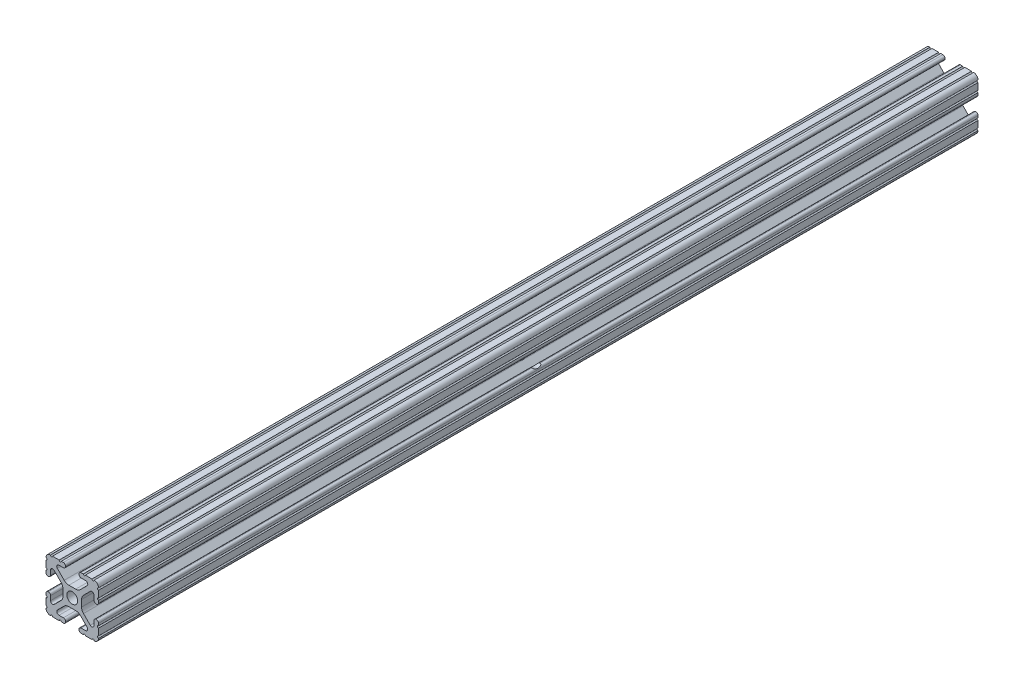
SolidWorks part; units mm, degrees
ref_plane "Front Plane" through (0, 0, 0) normal (0, 0, 1) x (1, 0, 0)
ref_plane "Top Plane" through (0, 0, 0) normal (0, 1, 0) x (1, 0, 0)
ref_plane "Right Plane" through (0, 0, 0) normal (1, 0, 0) x (0, 0, -1)
sketch "Sketch1" plane through (0, 0, 0) normal (0, 0, 1) x (1, 0, 0)
  line L88 (-7.1797, -8.6452) -> (-3.9523, -5.4237)
  line L89 (-1.7093, -4.4958) -> (1.7093, -4.4958)
  line L90 (3.9523, -5.4237) -> (7.1797, -8.6452)
  line L91 (6.4164, -10.4902) -> (4.2875, -10.4902)
  line L92 (3.2385, -11.5392) -> (3.2385, -11.651)
  line L93 (4.2875, -12.7) -> (5.3171, -12.7)
  line L94 (6.3331, -12.7) -> (9.5504, -12.7)
  line L95 (12.7, -9.5504) -> (12.7, -6.3331)
  line L96 (12.7, -5.3171) -> (12.7, -4.2875)
  line L97 (11.651, -3.2385) -> (11.5392, -3.2385)
  line L98 (10.4902, -4.2875) -> (10.4902, -6.4021)
  line L99 (8.7371, -7.1294) -> (5.441, -3.8408)
  line L100 (4.5085, -1.5932) -> (4.5085, 1.5932)
  line L101 (5.441, 3.8408) -> (8.7371, 7.1294)
  line L102 (10.4902, 6.4021) -> (10.4902, 4.2875)
  line L103 (11.5392, 3.2385) -> (11.651, 3.2385)
  line L104 (12.7, 4.2875) -> (12.7, 5.3171)
  line L105 (12.7, 6.3331) -> (12.7, 9.5504)
  line L106 (9.5504, 12.7) -> (6.3331, 12.7)
  line L107 (5.3171, 12.7) -> (4.2875, 12.7)
  line L108 (3.2385, 11.651) -> (3.2385, 11.5392)
  line L109 (4.2875, 10.4902) -> (6.4768, 10.4902)
  line L110 (7.207, 8.7244) -> (3.8983, 5.4232)
  line L111 (1.6558, 4.4958) -> (-1.6558, 4.4958)
  line L112 (-3.8983, 5.4232) -> (-7.207, 8.7244)
  line L113 (-6.4768, 10.4902) -> (-4.2875, 10.4902)
  line L114 (-3.2385, 11.5392) -> (-3.2385, 11.651)
  line L115 (-4.2875, 12.7) -> (-5.3171, 12.7)
  line L116 (-6.3331, 12.7) -> (-9.5504, 12.7)
  line L117 (-12.7, 9.5504) -> (-12.7, 6.3331)
  line L118 (-12.7, 5.3171) -> (-12.7, 4.2875)
  line L119 (-11.651, 3.2385) -> (-11.5392, 3.2385)
  line L120 (-10.4902, 4.2875) -> (-10.4902, 6.4021)
  line L121 (-8.7371, 7.1294) -> (-5.441, 3.8408)
  line L122 (-4.5085, 1.5932) -> (-4.5085, -1.5932)
  line L123 (-5.441, -3.8408) -> (-8.7371, -7.1294)
  line L124 (-10.4902, -6.4021) -> (-10.4902, -4.2875)
  line L125 (-11.5392, -3.2385) -> (-11.651, -3.2385)
  line L126 (-12.7, -4.2875) -> (-12.7, -5.3171)
  line L127 (-12.7, -6.3331) -> (-12.7, -9.5504)
  line L128 (-9.5504, -12.7) -> (-6.3331, -12.7)
  line L129 (-5.3171, -12.7) -> (-4.2875, -12.7)
  line L130 (-3.2385, -11.651) -> (-3.2385, -11.5392)
  line L131 (-4.2875, -10.4902) -> (-6.4164, -10.4902)
  circle A1 centre (0, 0) radius 2.6035
  arc A104 (-7.1797, -8.6452) -> (-6.4164, -10.4902) centre (-6.4164, -9.4098) ccw
  arc A105 (-1.7093, -4.4958) -> (-3.9523, -5.4237) centre (-1.7093, -7.6708) ccw
  arc A106 (3.9523, -5.4237) -> (1.7093, -4.4958) centre (1.7093, -7.6708) ccw
  arc A107 (6.4164, -10.4902) -> (7.1797, -8.6452) centre (6.4164, -9.4098) ccw
  arc A108 (4.2875, -10.4902) -> (3.2385, -11.5392) centre (4.2875, -11.5392) ccw
  arc A109 (3.2385, -11.651) -> (4.2875, -12.7) centre (4.2875, -11.651) ccw
  arc A110 (6.3331, -12.7) -> (5.3171, -12.7) centre (5.8251, -12.7) ccw
  arc A111 (10.5664, -12.6998) -> (9.5504, -12.7) centre (10.0584, -12.7) ccw
  arc A112 (10.5664, -12.6998) -> (12.6998, -10.5664) centre (10.5918, -10.5918) ccw
  arc A113 (12.7, -9.5504) -> (12.6998, -10.5664) centre (12.7, -10.0584) ccw
  arc A114 (12.7, -5.3171) -> (12.7, -6.3331) centre (12.7, -5.8251) ccw
  arc A115 (12.7, -4.2875) -> (11.651, -3.2385) centre (11.651, -4.2875) ccw
  arc A116 (11.5392, -3.2385) -> (10.4902, -4.2875) centre (11.5392, -4.2875) ccw
  arc A117 (8.7371, -7.1294) -> (10.4902, -6.4021) centre (9.4628, -6.4021) ccw
  arc A118 (4.5085, -1.5932) -> (5.441, -3.8408) centre (7.6835, -1.5932) ccw
  arc A119 (5.441, 3.8408) -> (4.5085, 1.5932) centre (7.6835, 1.5932) ccw
  arc A120 (10.4902, 6.4021) -> (8.7371, 7.1294) centre (9.4628, 6.4021) ccw
  arc A121 (10.4902, 4.2875) -> (11.5392, 3.2385) centre (11.5392, 4.2875) ccw
  arc A122 (11.651, 3.2385) -> (12.7, 4.2875) centre (11.651, 4.2875) ccw
  arc A123 (12.7, 6.3331) -> (12.7, 5.3171) centre (12.7, 5.8251) ccw
  arc A124 (12.6998, 10.5664) -> (12.7, 9.5504) centre (12.7, 10.0584) ccw
  arc A125 (12.6998, 10.5664) -> (10.5664, 12.6998) centre (10.5918, 10.5918) ccw
  arc A126 (9.5504, 12.7) -> (10.5664, 12.6998) centre (10.0584, 12.7) ccw
  arc A127 (5.3171, 12.7) -> (6.3331, 12.7) centre (5.8251, 12.7) ccw
  arc A128 (4.2875, 12.7) -> (3.2385, 11.651) centre (4.2875, 11.651) ccw
  arc A129 (3.2385, 11.5392) -> (4.2875, 10.4902) centre (4.2875, 11.5392) ccw
  arc A130 (7.207, 8.7244) -> (6.4768, 10.4902) centre (6.4768, 9.4563) ccw
  arc A131 (1.6558, 4.4958) -> (3.8983, 5.4232) centre (1.6558, 7.6708) ccw
  arc A132 (-3.8983, 5.4232) -> (-1.6558, 4.4958) centre (-1.6558, 7.6708) ccw
  arc A133 (-6.4768, 10.4902) -> (-7.207, 8.7244) centre (-6.4768, 9.4563) ccw
  arc A134 (-4.2875, 10.4902) -> (-3.2385, 11.5392) centre (-4.2875, 11.5392) ccw
  arc A135 (-3.2385, 11.651) -> (-4.2875, 12.7) centre (-4.2875, 11.651) ccw
  arc A136 (-6.3331, 12.7) -> (-5.3171, 12.7) centre (-5.8251, 12.7) ccw
  arc A137 (-10.5664, 12.6998) -> (-9.5504, 12.7) centre (-10.0584, 12.7) ccw
  arc A138 (-10.5664, 12.6998) -> (-12.6998, 10.5664) centre (-10.5918, 10.5918) ccw
  arc A139 (-12.7, 9.5504) -> (-12.6998, 10.5664) centre (-12.7, 10.0584) ccw
  arc A140 (-12.7, 5.3171) -> (-12.7, 6.3331) centre (-12.7, 5.8251) ccw
  arc A141 (-12.7, 4.2875) -> (-11.651, 3.2385) centre (-11.651, 4.2875) ccw
  arc A142 (-11.5392, 3.2385) -> (-10.4902, 4.2875) centre (-11.5392, 4.2875) ccw
  arc A143 (-8.7371, 7.1294) -> (-10.4902, 6.4021) centre (-9.4628, 6.4021) ccw
  arc A144 (-4.5085, 1.5932) -> (-5.441, 3.8408) centre (-7.6835, 1.5932) ccw
  arc A145 (-5.441, -3.8408) -> (-4.5085, -1.5932) centre (-7.6835, -1.5932) ccw
  arc A146 (-10.4902, -6.4021) -> (-8.7371, -7.1294) centre (-9.4628, -6.4021) ccw
  arc A147 (-10.4902, -4.2875) -> (-11.5392, -3.2385) centre (-11.5392, -4.2875) ccw
  arc A148 (-11.651, -3.2385) -> (-12.7, -4.2875) centre (-11.651, -4.2875) ccw
  arc A149 (-12.7, -6.3331) -> (-12.7, -5.3171) centre (-12.7, -5.8251) ccw
  arc A150 (-12.6998, -10.5664) -> (-12.7, -9.5504) centre (-12.7, -10.0584) ccw
  arc A151 (-12.6998, -10.5664) -> (-10.5664, -12.6998) centre (-10.5918, -10.5918) ccw
  arc A152 (-9.5504, -12.7) -> (-10.5664, -12.6998) centre (-10.0584, -12.7) ccw
  arc A153 (-5.3171, -12.7) -> (-6.3331, -12.7) centre (-5.8251, -12.7) ccw
  arc A154 (-4.2875, -12.7) -> (-3.2385, -11.651) centre (-4.2875, -11.651) ccw
  arc A155 (-3.2385, -11.5392) -> (-4.2875, -10.4902) centre (-4.2875, -11.5392) ccw
extrude "Boss-Extrude1" add sketch "Sketch1" along normal mid plane 425.45
sketch "Sketch2" plane through (-12.7, 0, 0) normal (-1, 0, 0) x (0, 0, 1)
  circle A0 centre (0, 0) radius 3.81
  point P2 (-3.6046, 0)
  point P4 (0, 0)
  dimension "D1" = 7.62
extrude "Cut-Extrude1" cut sketch "Sketch2" against normal blind 25.4
